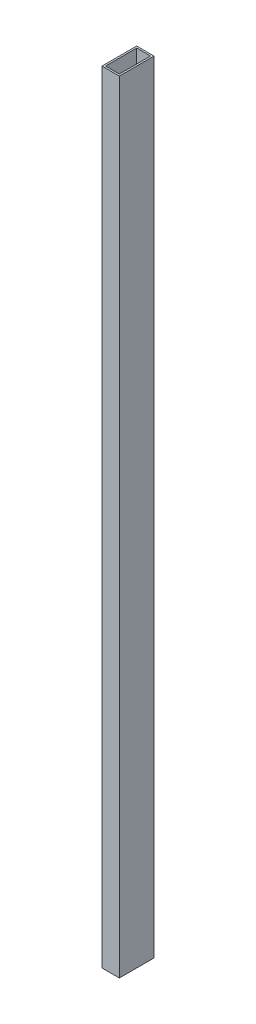
SolidWorks part; units mm, degrees
ref_plane "Спереди" through (0, 0, 0) normal (0, 0, 1) x (1, 0, 0)
ref_plane "Сверху" through (0, 0, 0) normal (0, 1, 0) x (1, 0, 0)
ref_plane "Справа" through (0, 0, 0) normal (1, 0, 0) x (0, 0, -1)
sketch "Sketch1" plane through (0, 0, 0) normal (0, 1, 0) x (1, 0, 0)
  line L1 (5, -10) -> (-5, -10)
  line L2 (5, -10) -> (5, 10)
  line L3 (5, 10) -> (-5, 10)
  line L4 (-5, -10) -> (-5, 10)
  line L5 (5, -10) -> (-5, 10) construction
  line L6 (5, 10) -> (-5, -10) construction
  line L7 (4, -9) -> (-4, -9)
  line L8 (4, -9) -> (4, 9)
  line L9 (4, 9) -> (-4, 9)
  line L10 (-4, -9) -> (-4, 9)
  line L11 (4, -9) -> (-4, 9) construction
  line L12 (4, 9) -> (-4, -9) construction
  point P0 (0, 0)
  point P6 (0, 0)
  dimension "D1" = 10
  dimension "D2" = 20
  dimension "D3" = 1
  dimension "D4" = 1
extrude "Boss-Extrude1" add sketch "Sketch1" along normal blind 450
